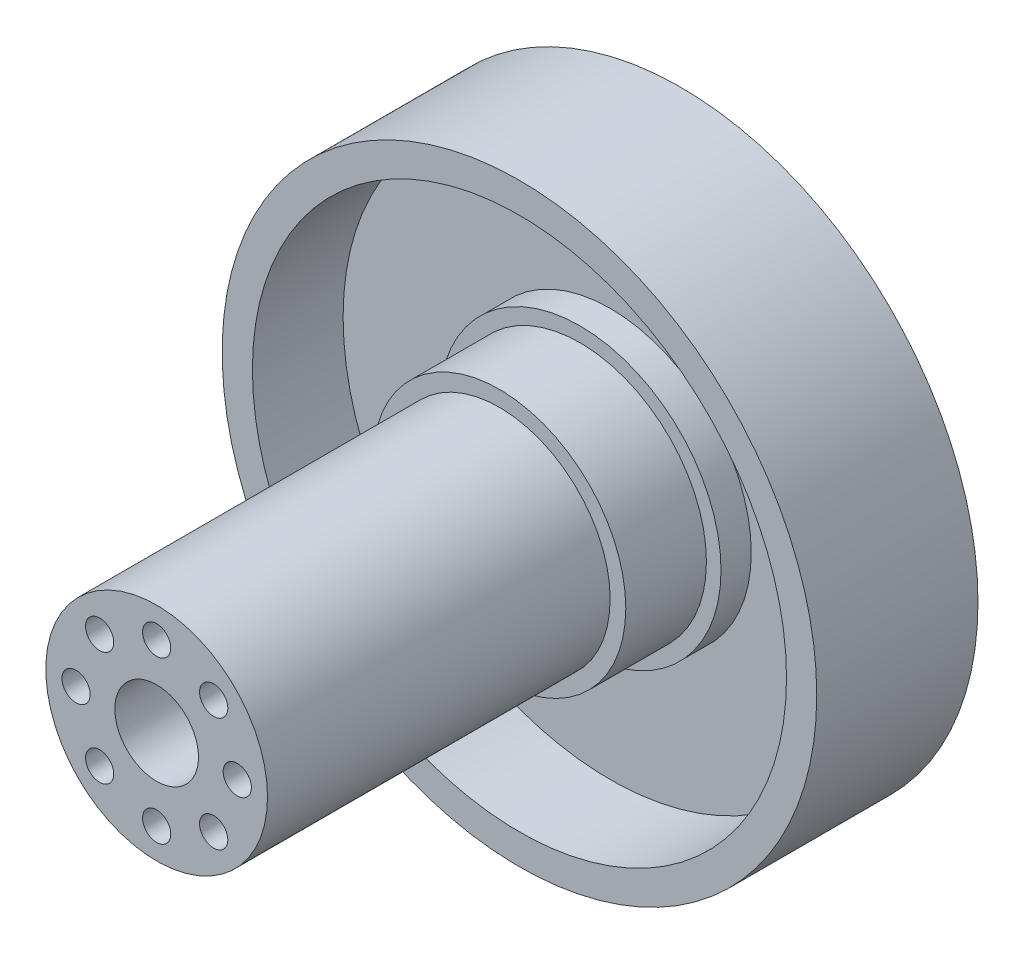
SolidWorks part; units mm, degrees
ref_plane "Front Plane" through (0, 0, 0) normal (0, 0, 1) x (1, 0, 0)
ref_plane "Top Plane" through (0, 0, 0) normal (0, 1, 0) x (1, 0, 0)
ref_plane "Right Plane" through (0, 0, 0) normal (1, 0, 0) x (0, 0, -1)
sketch "Sketch2" plane through (0, 0, 0) normal (0, 0, 1) x (1, 0, 0)
  circle A0 centre (0, 0) radius 29.5
  dimension "D1" = 59
extrude "Boss-Extrude1" add sketch "Sketch2" along normal blind 7
sketch "Sketch3" plane through (0, 0, 7) normal (0, 0, 1) x (1, 0, 0)
  circle A0 centre (0, 0) radius 14
  dimension "D1" = 28
extrude "Boss-Extrude2" add sketch "Sketch3" along normal blind 3
sketch "Sketch5" plane through (0, 0, 10) normal (0, 0, 1) x (1, 0, 0)
  circle A0 centre (0, 0) radius 12.55
  dimension "D1" = 25.1
extrude "Boss-Extrude3" add sketch "Sketch5" along normal blind 8
sketch "Sketch6" plane through (0, 0, 18) normal (0, 0, 1) x (1, 0, 0)
  circle A0 centre (0, 0) radius 11
  dimension "D1" = 22
extrude "Boss-Extrude4" add sketch "Sketch6" along normal blind 34
sketch "Sketch7" plane through (0, 0, 0) normal (0, 0, -1) x (-1, 0, 0)
  circle A0 centre (0, 0) radius 2.8234
  circle A1 centre (8, 0) radius 2.1
  circle A2 centre (5.6569, -5.6569) radius 2.1
  circle A3 centre (0, -8) radius 2.1
  circle A4 centre (-5.6569, -5.6569) radius 2.1
  circle A5 centre (-8, 0) radius 2.1
  circle A6 centre (-5.6569, 5.6569) radius 2.1
  circle A7 centre (0, 8) radius 2.1
  circle A8 centre (5.6569, 5.6569) radius 2.1
  point P22 (0, 0)
  dimension "D1" = 4.2
  dimension "D2" = 8
  dimension "D3" = 8
extrude "Cut-Extrude1" cut sketch "Sketch7" against normal blind 33.8 contours A4 | A5 | A6 | A7 | A8 | A1 | A2 | A3
sketch "Sketch8" plane through (0, 0, 33.8) normal (0, 0, -1) x (-1, 0, 0)
  circle A0 centre (-8, 0) radius 1.4
  circle A1 centre (-5.6569, 5.6569) radius 1.4
  circle A2 centre (0, 8) radius 1.4
  circle A3 centre (5.6569, 5.6569) radius 1.4
  circle A4 centre (8, 0) radius 1.4
  circle A5 centre (5.6569, -5.6569) radius 1.4
  circle A6 centre (0, -8) radius 1.4
  circle A7 centre (-5.6569, -5.6569) radius 1.4
  point P20 (0, 0)
  dimension "D1" = 2.8
  dimension "D2" = 8
extrude "Cut-Extrude2" cut sketch "Sketch8" against normal through all
sketch "Sketch9" plane through (0, 0, 52) normal (0, 0, 1) x (1, 0, 0)
  circle A0 centre (0, 0) radius 4.15
  dimension "D1" = 8.3
extrude "Cut-Extrude3" cut sketch "Sketch9" against normal blind 9
sketch "Sketch10" plane through (0, 0, 0) normal (0, 0, 1) x (1, 0, 0)
  circle A0 centre (-26, 0) radius 2.07
  circle A1 centre (0, 0) radius 14 construction
  circle A8 centre (0, 26) radius 2.07
  circle A9 centre (26, 0) radius 2.07
  circle A10 centre (0, -26) radius 2.07
  point P13 (-0.875, -0.875)
  point P14 (-2.5, -2.5)
  point P15 (0, 0)
  dimension "D1" = 4.14
  dimension "D2" = 26
  dimension "D3" = 4
extrude "Cut-Extrude4" cut sketch "Sketch10" along normal blind 5
sketch "Sketch11" plane through (0, 0, 7) normal (0, 0, 1) x (1, 0, 0)
  circle A0 centre (0, 0) radius 29.5
  circle A1 centre (0, 0) radius 26.5
  dimension "D1" = 53
extrude "Boss-Extrude5" add sketch "Sketch11" along normal blind 9
